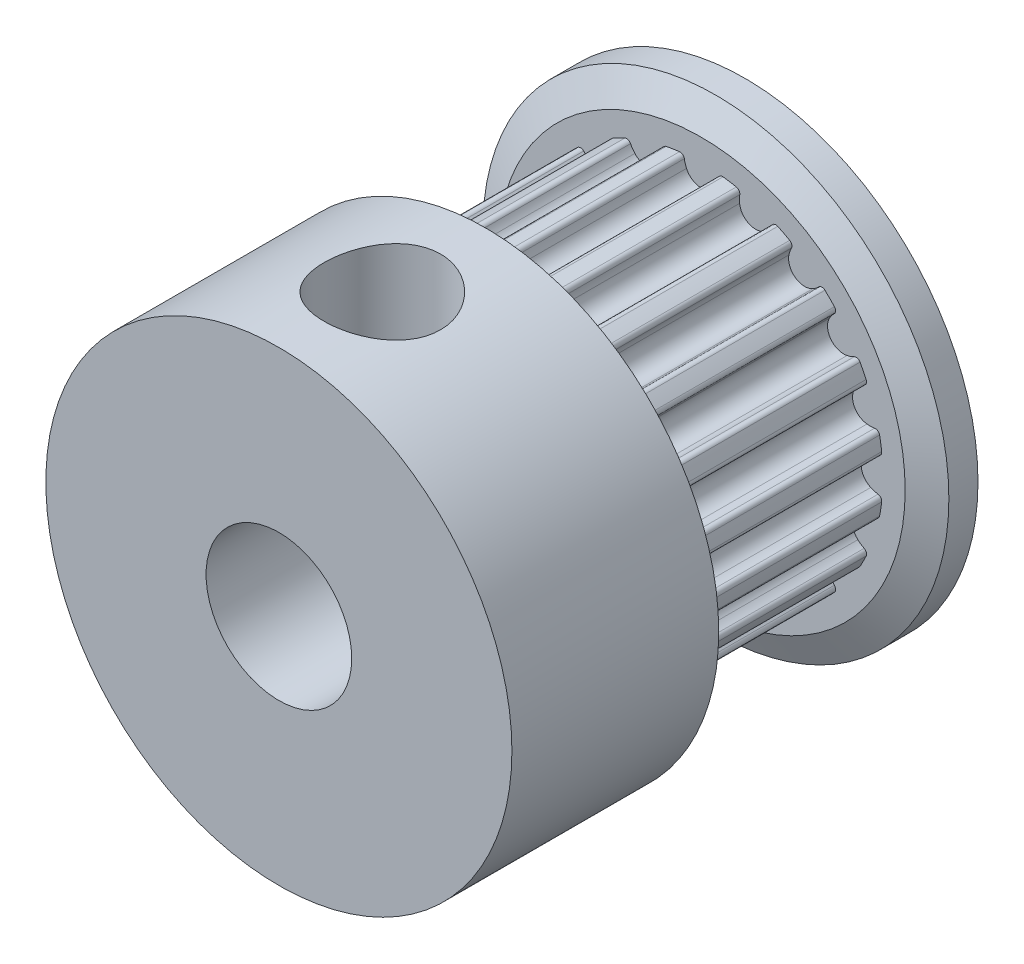
SolidWorks part; units mm, degrees
ref_plane "Front Plane" through (0, 0, 0) normal (0, 0, 1) x (1, 0, 0)
ref_plane "Top Plane" through (0, 0, 0) normal (0, 1, 0) x (1, 0, 0)
ref_plane "Right Plane" through (0, 0, 0) normal (1, 0, 0) x (0, 0, -1)
sketch "Sketch1" plane through (0, 0, 0) normal (0, 0, 1) x (1, 0, 0)
  circle A0 centre (0, 0) radius 6.366
  dimension "D1" = 12.732
extrude "Base" add sketch "Sketch1" along normal blind 7.4
sketch "Sketch2" plane through (0, 0, 7.4) normal (0, 0, 1) x (1, 0, 0)
  line L0 (0, 0) -> (0, 6.239) construction
  line L1 (0, 0) -> (-1.928, 5.9336) construction
  line L2 (-0.976, 6.1622) -> (0, 0) construction
  line L3 (-0.976, 6.1622) -> (-0.9959, 6.2876)
  line L4 (0.976, 6.1622) -> (0.9959, 6.2876)
  arc A1 (-0.5814, 6.0687) -> (-0.5066, 5.8173) centre (0.4062, 6.2258) ccw
  arc A2 (-0.5066, 5.8173) -> (0.5066, 5.8173) centre (0, 6.044) ccw
  arc A3 (-0.5814, 6.0687) -> (-0.7475, 6.1941) centre (-0.7295, 6.0451) ccw
  arc A4 (0.5814, 6.0687) -> (0.5066, 5.8173) centre (-0.4062, 6.2258) cw
  arc A5 (0.5814, 6.0687) -> (0.7475, 6.1941) centre (0.7295, 6.0451) cw
  arc A6 (0.7475, 6.1941) -> (0.976, 6.1622) centre (0, 0) cw
  circle A7 centre (0, 0) radius 6.366 construction
  arc A8 (0.9959, 6.2876) -> (-0.9959, 6.2876) centre (0, 0) ccw
  arc A11 (-0.7475, 6.1941) -> (-0.976, 6.1622) centre (0, 0) ccw
  dimension "D1" = 6.239
  dimension "D3" = 2
  dimension "D4" = 1.11
  dimension "D7" = 0.3
  dimension "D2" = 18
  dimension "D5" = 0.195
  dimension "D6" = 9
  dimension "D8" = 0.4062
extrude "ToothCut" cut sketch "Sketch2" against normal through all
pattern_circular "TeethCuts" count 20 over 360 about axis through (0, 0, 0) along (0, 0, 1) of "ToothCut"
sketch "Sketch3" plane through (0, 0, 0) normal (0, 1, 0) x (1, 0, 0)
  line L0 (0, 0) -> (0, 1.5)
  line L1 (0, 1.5) -> (-8, 1.5)
  line L2 (-8, 1.5) -> (-8, 0.5)
  line L3 (-7, 0) -> (0, 0)
  line L4 (0, -7.4) -> (-8, -7.4)
  line L5 (-0.5066, -7.4) -> (0.5066, -7.4) construction
  line L6 (-8, -7.4) -> (-8, -14.5)
  line L7 (-8, -14.5) -> (0, -14.5)
  line L8 (0, -14.5) -> (0, -7.4)
  line L9 (-8, 0.5) -> (-7, 0)
  point P5 (-8, 0)
  dimension "D1" = 16
  dimension "D2" = 1.5
  dimension "D3" = 0.5
  dimension "D4" = 1
  dimension "D5" = 8
revolve "Body" add sketch "Sketch3" angle 360 about L8
sketch "Sketch4" plane through (0, 0, 0) normal (0, 0, 1) x (1, 0, 0)
  circle A0 centre (0, 0) radius 2.5
  dimension "D1" = 5
extrude "ShaftHole" cut sketch "Sketch4" along normal through all both and the other way through all
sketch "Sketch5" plane through (0, 0, 0) normal (0, 1, 0) x (1, 0, 0)
  line L0 (-8, -7.4) -> (-8, -14.5) construction
  line L3 (-8, -14.5) -> (8, -14.5) construction
  circle A0 centre (0, -10.95) radius 2
  point P4 (0, 0)
  dimension "D1" = 4
  dimension "D2" = 8
  dimension "D3" = 3.55
extrude "FixingHole" cut sketch "Sketch5" along normal through all
